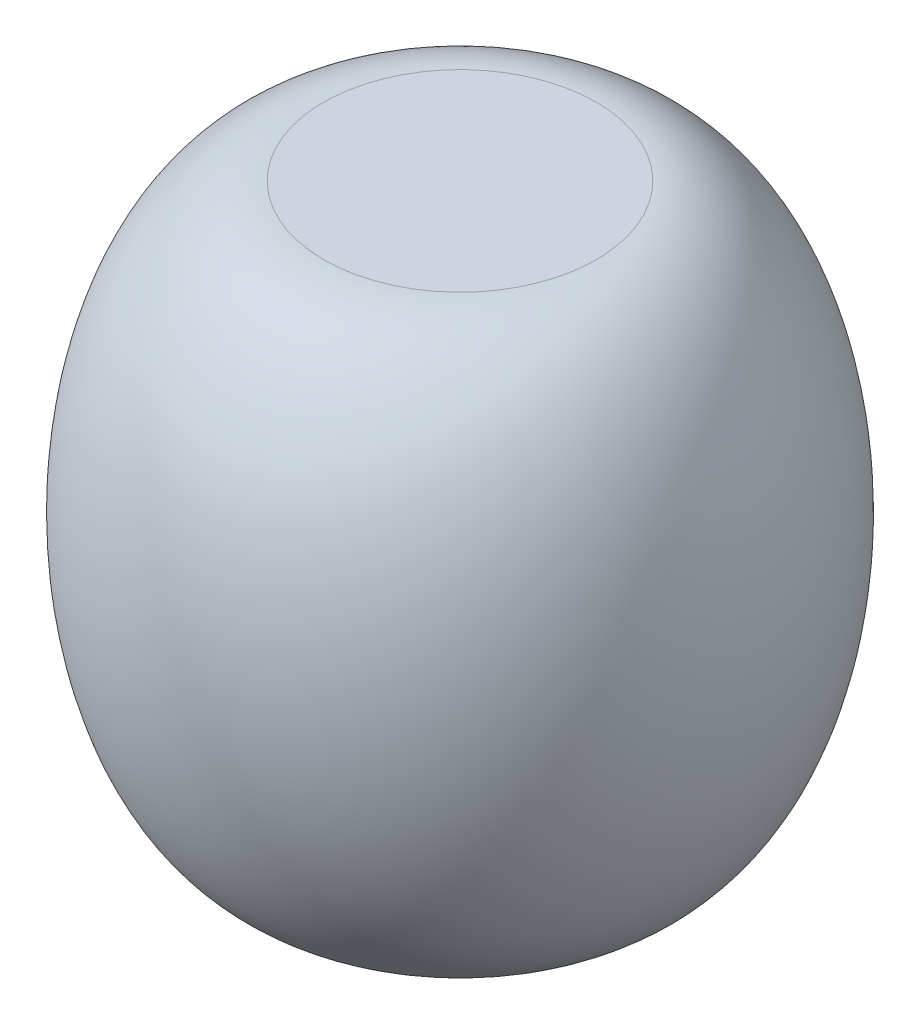
SolidWorks part; units mm, degrees
ref_plane "Alzado" through (0, 0, 0) normal (0, 0, 1) x (1, 0, 0)
ref_plane "Planta" through (0, 0, 0) normal (0, 1, 0) x (1, 0, 0)
ref_plane "Vista lateral" through (0, 0, 0) normal (1, 0, 0) x (0, 0, -1)
sketch "Croquis1" plane through (0, 0, 0) normal (0, 0, 1) x (1, 0, 0)
  line L0 (0, 0) -> (0, 51)
  line L1 (0, 51) -> (12.1296, 51)
  line L2 (0, 25.5) -> (13.5, 25.5) construction
  line L3 (0, 0) -> (12.1296, 0)
  line L4 (13.5, 51) -> (13.5, 0) construction
  ellipse E0 centre (12.1296, 25.5) end of major axis (12.1296, 51) minor radius 13.8704 (12.1296, 0) -> (12.1296, 51) ccw
  dimension "D1" = 51
  dimension "D2" = 13.5
  dimension "D3" = 26
  dimension "D4" = 12.1296
  dimension "D5" = 12.1296
revolve "Revolución1" add sketch "Croquis1" angle 360 about L0
